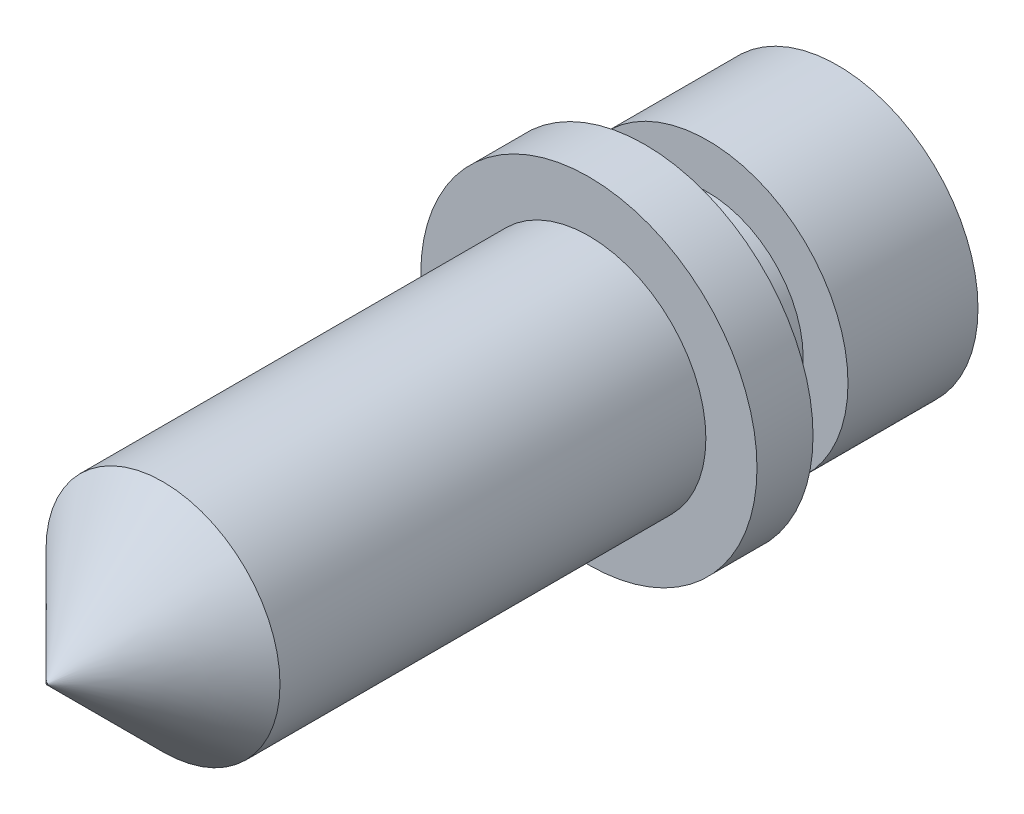
SolidWorks part; units mm, degrees
material "Brass"
ref_plane "Front Plane" through (0, 0, 0) normal (0, 0, 1) x (1, 0, 0)
ref_plane "Top Plane" through (0, 0, 0) normal (0, 1, 0) x (1, 0, 0)
ref_plane "Right Plane" through (0, 0, 0) normal (1, 0, 0) x (0, 0, -1)
sketch "Sketch1" plane through (0, 0, 0) normal (0, 0, 1) x (1, 0, 0)
  circle A0 centre (0, 0) radius 4.7625
  dimension "D1" = 9.525
extrude "Boss-Extrude1" add sketch "Sketch1" along normal mid plane 1.5875
sketch "Sketch2" plane through (0, 0, -0.7937) normal (0, 0, -1) x (-1, 0, 0)
  circle A0 centre (0, 0) radius 3.9751
  dimension "D1" = 7.9502
extrude "Boss-Extrude2" add sketch "Sketch2" along normal blind 5.461
sketch "Sketch3" plane through (0, 0, 0.7937) normal (0, 0, 1) x (1, 0, 0)
  circle A0 centre (0, 0) radius 3.3147
  dimension "D1" = 6.6294
extrude "Boss-Extrude3" add sketch "Sketch3" along normal blind 12.065
sketch "Sketch4" plane through (0, 0, 0) normal (1, 0, 0) x (0, 0, -1)
  line L0 (0, 0) -> (-11.7022, 0) construction
sketch "Sketch5" plane through (0, 0, 0) normal (1, 0, 0) x (0, 0, -1)
  line L0 (-12.8587, 3.3147) -> (-16.1734, 0)
  line L1 (0, 0) -> (-11.7022, 0) construction
  line L2 (-16.1734, 0) -> (-12.8587, 0)
  line L3 (-12.8587, 3.3147) -> (-12.8587, -3.3147) construction
  line L4 (-12.8587, 0) -> (-12.8587, 3.3147)
  dimension "D1" = 45
revolve "Revolve1" add sketch "Sketch5" angle 360 about L0
sketch "Sketch6" plane through (0, 0, -6.2547) normal (0, 0, -1) x (-1, 0, 0)
  circle A0 centre (0, 0) radius 1.5875
  dimension "D1" = 3.175
extrude "Cut-Extrude1" cut sketch "Sketch6" against normal blind 19.05
sketch "Sketch10" plane through (0, 0, 0) normal (0, 1, 0) x (1, 0, 0)
  line L0 (-3.9751, 6.2547) -> (-3.9751, 0.7938) construction
  line L1 (-3.9751, 0.7938) -> (-2.7051, 0.7938)
  line L2 (-3.9751, 0.7938) -> (-3.9751, 2.5718)
  line L3 (-3.9751, 2.5718) -> (-2.7051, 2.5718)
  line L4 (-2.7051, 0.7938) -> (-2.7051, 2.5718)
  line L5 (3.9751, 0.7938) -> (-3.9751, 0.7938) construction
  line L6 (0, 0) -> (0, 6.2547) construction
  line L7 (1.5875, 6.2547) -> (-1.5875, 6.2547) construction
  dimension "D1" = 1.778
  dimension "D2" = 1.27
revolve "Cut-Revolve1" cut sketch "Sketch10" angle 360 about L6
ref_plane "Plane2" through (0, 0, 16.1734) normal (0, 0, 1) x (1, 0, 0)
sketch "Sketch11" plane through (0, 0, 16.1734) normal (0, 0, 1) x (1, 0, 0)
  circle A0 centre (0, 0) radius 0.0508
extrude "Cut-Extrude3" cut sketch "Sketch11" against normal blind 0.0254
sketch "Sketch9" plane through (0, 0, -6.2547) normal (0, 0, -1) x (-1, 0, 0)
  circle A0 centre (0, 0) radius 0.02
  dimension "D1" = 0.04
extrude "Cut-Extrude2" cut sketch "Sketch9" against normal through all
